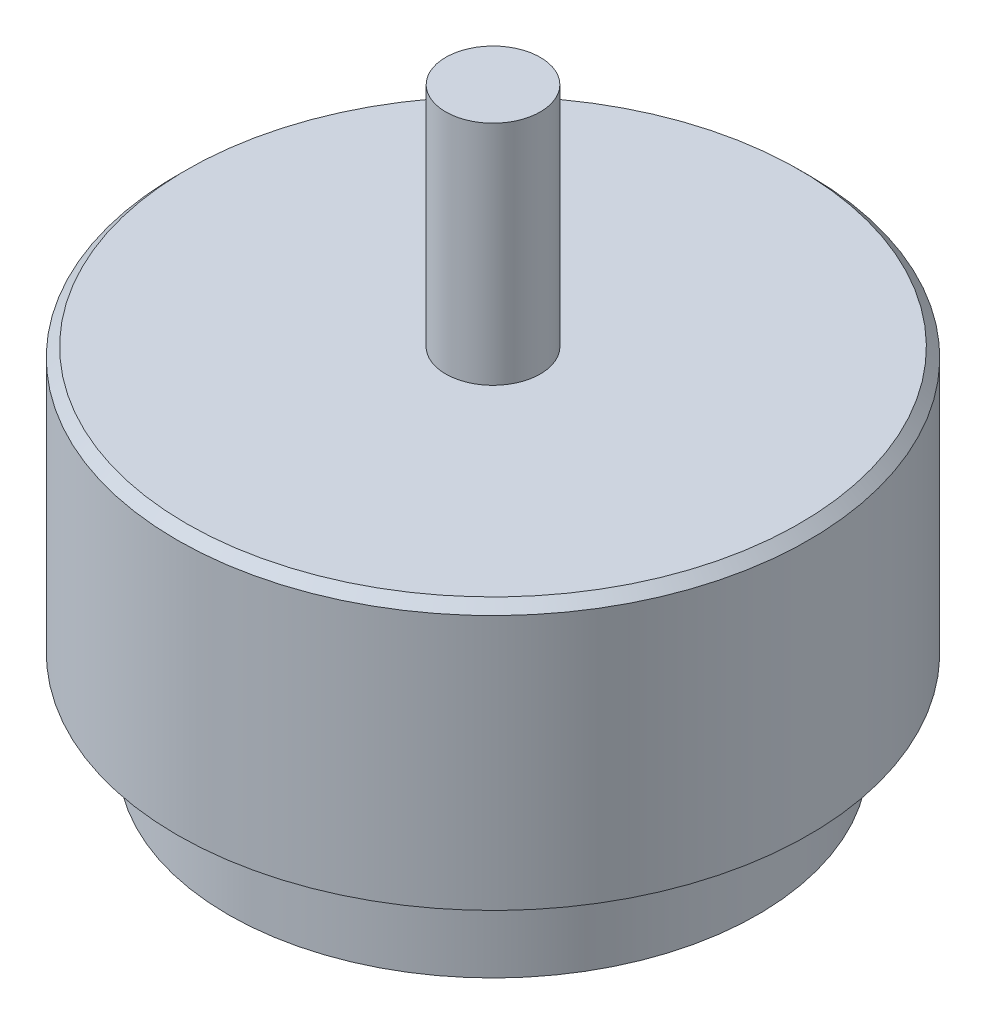
SolidWorks part; units mm, degrees
material "6061-T6 (SS)"
ref_plane "Front Plane" through (0, 0, 0) normal (0, 0, 1) x (1, 0, 0)
ref_plane "Top Plane" through (0, 0, 0) normal (0, 1, 0) x (1, 0, 0)
ref_plane "Right Plane" through (0, 0, 0) normal (1, 0, 0) x (0, 0, -1)
sketch "Sketch1" plane through (0, 0, 0) normal (0, 1, 0) x (1, 0, 0)
  circle A0 centre (0, 0) radius 14
  dimension "D1" = 28
extrude "Boss-Extrude1" add sketch "Sketch1" along normal blind 5
sketch "Sketch2" plane through (0, 5, 0) normal (0, 1, 0) x (1, 0, 0)
  circle A0 centre (0, 0) radius 16.7
  dimension "D1" = 33.4
extrude "Boss-Extrude2" add sketch "Sketch2" along normal blind 14
sketch "Sketch3" plane through (0, 19, 0) normal (0, 1, 0) x (1, 0, 0)
  circle A0 centre (0, 0) radius 2.5
  dimension "D1" = 5
extrude "Boss-Extrude3" add sketch "Sketch3" along normal blind 12
chamfer "Chamfer1" distance 0.5 angle 45 1 edges at (0, 19, 16.7)
sketch "Sketch4" plane through (0, 0, 0) normal (0, -1, 0) x (1, 0, 0)
  circle A0 centre (0, 0) radius 7
  dimension "D1" = 14
extrude "Cut-Extrude1" cut sketch "Sketch4" against normal blind 6
